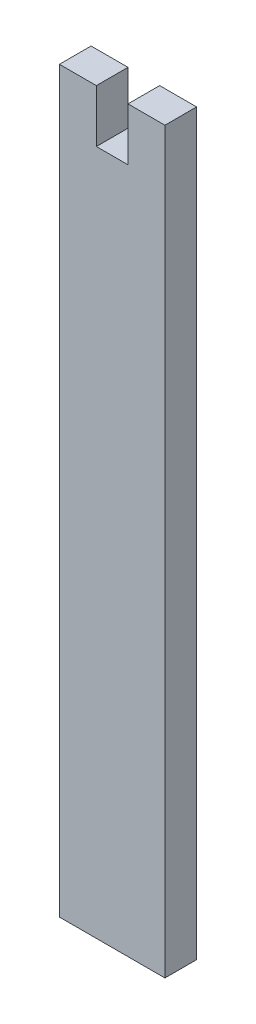
SolidWorks part; units mm, degrees
ref_plane "Front Plane" through (0, 0, 0) normal (0, 0, 1) x (1, 0, 0)
ref_plane "Top Plane" through (0, 0, 0) normal (0, 1, 0) x (1, 0, 0)
ref_plane "Right Plane" through (0, 0, 0) normal (1, 0, 0) x (0, 0, -1)
sketch "Sketch1" plane through (0, 0, 0) normal (0, 0, 1) x (1, 0, 0)
  line L0 (-5, -32) -> (5, -32) construction
  line L1 (-5, 35) -> (5, 35)
  line L2 (-5, 35) -> (-5, -35)
  line L3 (-5, -35) -> (5, -35)
  line L4 (5, 35) -> (5, -35)
  line L5 (-5, 35) -> (5, -35) construction
  line L6 (-5, -35) -> (5, 35) construction
  line L7 (-1.5, 35) -> (1.5, 35)
  line L8 (-1.5, 35) -> (-1.5, 30)
  line L9 (-1.5, 30) -> (1.5, 30)
  line L10 (1.5, 35) -> (1.5, 30)
  point P0 (0, 0)
  dimension "D1" = 3
  dimension "D2" = 5
  dimension "D3" = 70
  dimension "D4" = 10
  dimension "D5" = 3.5
  dimension "D6" = 3
extrude "Boss-Extrude1" add sketch "Sketch1" along normal mid plane 3 contours L1 L10 L9 L8 L2 L3 L4
